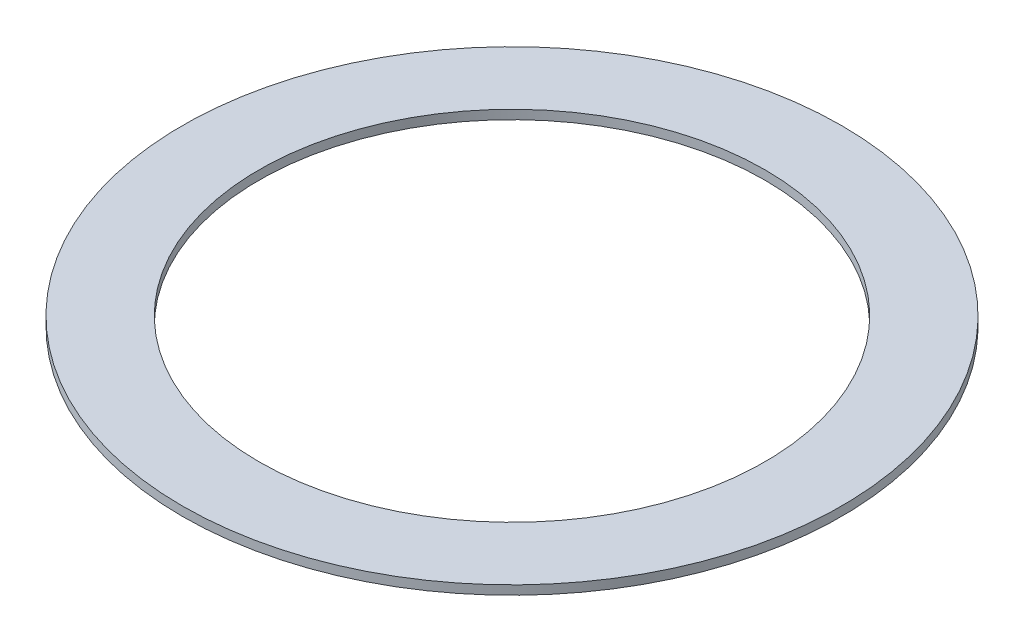
SolidWorks part; units mm, degrees
ref_plane "Front Plane" through (0, 0, 0) normal (0, 0, 1) x (1, 0, 0)
ref_plane "Top Plane" through (0, 0, 0) normal (0, 1, 0) x (1, 0, 0)
ref_plane "Right Plane" through (0, 0, 0) normal (1, 0, 0) x (0, 0, -1)
sketch "Sketch1" plane through (0, 0, 0) normal (0, 1, 0) x (1, 0, 0)
  circle A0 centre (0, 0) radius 88.9
  circle A1 centre (0, 0) radius 115.824
  dimension "D1" = 177.8
  dimension "D2" = 231.648
extrude "Boss-Extrude1" add sketch "Sketch1" along normal blind 3.175
equation "\"2x3.5\"=3.60815"
